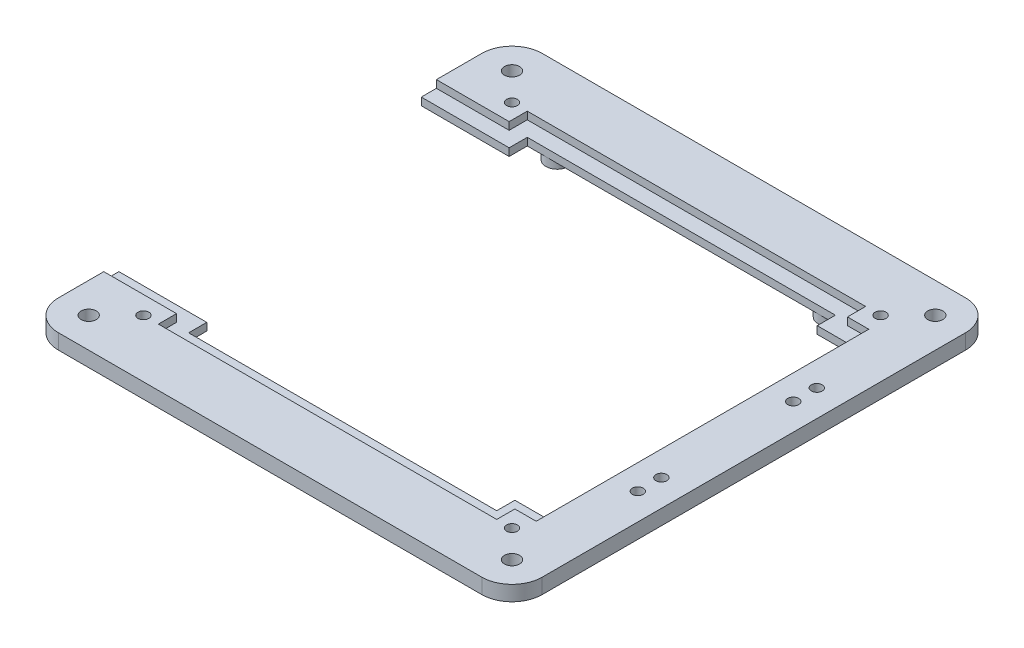
SolidWorks part; units mm, degrees
ref_plane "Front Plane" through (0, 0, 0) normal (0, 0, 1) x (1, 0, 0)
ref_plane "Top Plane" through (0, 0, 0) normal (0, 1, 0) x (1, 0, 0)
ref_plane "Right Plane" through (0, 0, 0) normal (1, 0, 0) x (0, 0, -1)
sketch "Sketch1" plane through (0, 0, 0) normal (0, 1, 0) x (1, 0, 0)
  line L0 (0, 0) -> (0, 25.4)
  line L1 (12.7, 38.1) -> (190.5, 38.1)
  line L2 (203.2, 25.4) -> (203.2, -152.4)
  line L3 (190.5, -165.1) -> (12.7, -165.1)
  line L4 (0, -152.4) -> (0, -127)
  line L5 (0, -127) -> (181.61, -127)
  line L6 (181.61, -127) -> (181.61, 0)
  line L7 (181.61, 0) -> (0, 0)
  arc A0 (12.7, -165.1) -> (0, -152.4) centre (12.7, -152.4) cw
  arc A1 (203.2, -152.4) -> (190.5, -165.1) centre (190.5, -152.4) cw
  arc A2 (190.5, 38.1) -> (203.2, 25.4) centre (190.5, 25.4) cw
  arc A3 (0, 25.4) -> (12.7, 38.1) centre (12.7, 25.4) cw
  point P13 (203.2, -165.1)
  point P16 (203.2, 38.1)
  point P19 (0, 38.1)
  dimension "D6" = 12.7
  dimension "D1" = 203.2
  dimension "D2" = 38.1
  dimension "D3" = 203.2
  dimension "D4" = 181.61
  dimension "D5" = 127
extrude "Boss-Extrude2" add sketch "Sketch1" along normal blind 6.35
sketch "Sketch2" plane through (0, 6.35, 0) normal (0, 1, 0) x (1, 0, 0)
  circle A0 centre (12.7, 25.4) radius 3.175
  circle A1 centre (190.5, 25.4) radius 3.175
  circle A2 centre (190.5, -152.4) radius 3.175
  circle A3 centre (12.7, -152.4) radius 3.175
  arc A4 (12.7, 38.1) -> (0, 25.4) centre (12.7, 25.4) ccw construction
  dimension "D1" = 6.35
extrude "Cut-Extrude1" cut sketch "Sketch2" against normal through all
sketch "Sketch7" plane through (0, 6.35, 0) normal (0, 1, 0) x (1, 0, 0)
  line L0 (192.024, -28.194) -> (192.024, -33.528) construction
  line L1 (192.024, -38.1) -> (192.024, -88.9) construction
  line L2 (192.024, -93.472) -> (192.024, -98.806) construction
  line L3 (192.024, -23.622) -> (192.024, 38.1) construction
  line L4 (190.5, 38.1) -> (12.7, 38.1) construction
  line L5 (192.024, -103.378) -> (192.024, -165.1) construction
  line L6 (12.7, -165.1) -> (190.5, -165.1) construction
  line L7 (189.738, -25.908) -> (181.61, -25.908) construction
  line L8 (181.61, 0) -> (181.61, -127) construction
  circle A0 centre (192.024, -101.092) radius 2.286
  circle A1 centre (192.024, -91.186) radius 2.286
  circle A2 centre (192.024, -35.814) radius 2.286
  circle A3 centre (192.024, -25.908) radius 2.286
  dimension "D1" = 4.572
  dimension "D2" = 5.334
  dimension "D3" = 5.334
  dimension "D4" = 50.8
  dimension "D5" = 8.128
extrude "Cut-Extrude3" cut sketch "Sketch7" against normal blind 12.7
sketch "Sketch8" plane through (0, 0, 0) normal (0, -1, 0) x (-1, 0, 0)
  line L0 (-3.7197, -161.3803) -> (-199.4803, 34.3803) construction
  line L1 (-24.1978, 13.9022) -> (-24.1978, 38.1) construction
  line L2 (-190.5, 38.1) -> (-12.7, 38.1) construction
  line L3 (-24.1978, 13.9022) -> (0, 13.9022) construction
  line L5 (-24.1978, 13.9022) -> (-3.7197, 34.3803) construction
  line L6 (0, 25.4) -> (0, 0) construction
  arc A0 (0, 25.4) -> (-12.7, 38.1) centre (-12.7, 25.4) ccw construction
  circle A1 centre (-24.1978, 13.9022) radius 2.286
  arc A2 (-12.7, -165.1) -> (0, -152.4) centre (-12.7, -152.4) ccw construction
  arc A3 (-190.5, 38.1) -> (-203.2, 25.4) centre (-190.5, 25.4) ccw construction
  circle A4 centre (-24.1978, -140.9022) radius 2.286
  circle A5 centre (-179.0022, -140.9022) radius 2.286
  circle A6 centre (-179.0022, 13.9022) radius 2.286
  point P8 (-101.6, -63.5)
  dimension "D2" = 4.572
  dimension "D1" = 28.9603
  dimension "D3" = 4
extrude "Cut-Extrude4" cut sketch "Sketch8" against normal through all
sketch "Sketch9" plane through (0, 6.35, 0) normal (0, 1, 0) x (1, 0, 0)
  line L0 (0, 0) -> (181.61, 0) construction
  line L1 (36.8978, 0) -> (166.3022, 0)
  line L2 (36.8978, 0) -> (36.8978, 7.62)
  line L3 (36.8978, 7.62) -> (166.3022, 7.62)
  line L4 (166.3022, 0) -> (166.3022, 7.62)
  line L5 (181.61, -127) -> (0, -127) construction
  line L6 (166.3022, -127) -> (36.8978, -127)
  line L7 (166.3022, -127) -> (166.3022, -134.62)
  line L8 (166.3022, -134.62) -> (36.8978, -134.62)
  line L9 (36.8978, -127) -> (36.8978, -134.62)
  line L10 (12.7, -165.1) -> (190.5, -165.1) construction
  line L11 (190.5, 38.1) -> (12.7, 38.1) construction
  circle A0 centre (179.0022, 13.9022) radius 2.286 construction
  circle A1 centre (24.1978, 13.9022) radius 2.286 construction
  point P12 (101.6, -134.62)
  point P15 (101.6, -165.1)
  dimension "D1" = 12.7
  dimension "D2" = 12.7
  dimension "D3" = 30.48
extrude "Cut-Extrude5" cut sketch "Sketch9" against normal through all
sketch "Sketch10" plane through (0, 0, 0) normal (0, -1, 0) x (-1, 0, 0)
  line L0 (-203.2, -152.4) -> (-203.2, 25.4) construction
  line L1 (-12.7, -165.1) -> (-190.5, -165.1) construction
  line L2 (-190.5, 38.1) -> (-12.7, 38.1) construction
  line L3 (0, 25.4) -> (0, 0) construction
  circle A0 centre (-44.45, -139.7) radius 2.286
  circle A1 centre (-158.75, -139.7) radius 2.286
  circle A2 centre (-158.75, 12.7) radius 2.286
  circle A3 centre (-44.45, 12.7) radius 2.286
  circle A4 centre (-44.45, 12.7) radius 4.826
  circle A5 centre (-158.75, 12.7) radius 4.826
  circle A6 centre (-158.75, -139.7) radius 4.826
  circle A7 centre (-44.45, -139.7) radius 4.826
  dimension "D1" = 4.572
  dimension "D2" = 44.45
  dimension "D3" = 25.4
  dimension "D4" = 25.4
  dimension "D5" = 44.45
  dimension "D6" = 2.54
extrude "Boss-Extrude3" add sketch "Sketch10" along normal blind 3.81
sketch "Sketch11" plane through (0, 6.35, 0) normal (0, 1, 0) x (1, 0, 0)
  line L0 (0, 0) -> (36.8978, 0)
  line L1 (36.8978, 0) -> (36.8978, 7.62)
  line L2 (36.8978, 7.62) -> (166.3022, 7.62)
  line L3 (166.3022, 7.62) -> (166.3022, 0)
  line L4 (166.3022, 0) -> (181.61, 0)
  line L5 (181.61, 0) -> (181.61, 6.35)
  line L6 (181.61, 6.35) -> (172.6522, 6.35)
  line L7 (172.6522, 6.35) -> (172.6522, 13.97)
  line L8 (172.6522, 13.97) -> (30.5478, 13.97)
  line L9 (30.5478, 13.97) -> (30.5478, 6.35)
  line L10 (30.5478, 6.35) -> (0, 6.35)
  line L11 (0, 25.4) -> (0, 0) construction
  line L12 (0, 6.35) -> (0, 0)
  line L13 (-818.39, -63.5) -> (49181.61, -63.5) construction
  line L14 (181.61, 0) -> (181.61, -127) construction
  line L15 (0, -133.35) -> (0, -127)
  line L16 (30.5478, -133.35) -> (0, -133.35)
  line L17 (30.5478, -140.97) -> (30.5478, -133.35)
  line L18 (172.6522, -140.97) -> (30.5478, -140.97)
  line L19 (172.6522, -133.35) -> (172.6522, -140.97)
  line L20 (181.61, -133.35) -> (172.6522, -133.35)
  line L21 (181.61, -127) -> (181.61, -133.35)
  line L22 (166.3022, -127) -> (181.61, -127)
  line L23 (166.3022, -134.62) -> (166.3022, -127)
  line L24 (36.8978, -134.62) -> (166.3022, -134.62)
  line L25 (36.8978, -127) -> (36.8978, -134.62)
  line L26 (0, -127) -> (36.8978, -127)
  point P25 (181.61, -63.5)
  dimension "D1" = 6.35
  dimension "D2" = 6.35
  dimension "D3" = 6.35
  dimension "D4" = 6.35
  dimension "D5" = 6.35
extrude "Cut-Extrude6" cut sketch "Sketch11" against normal blind 3.175
